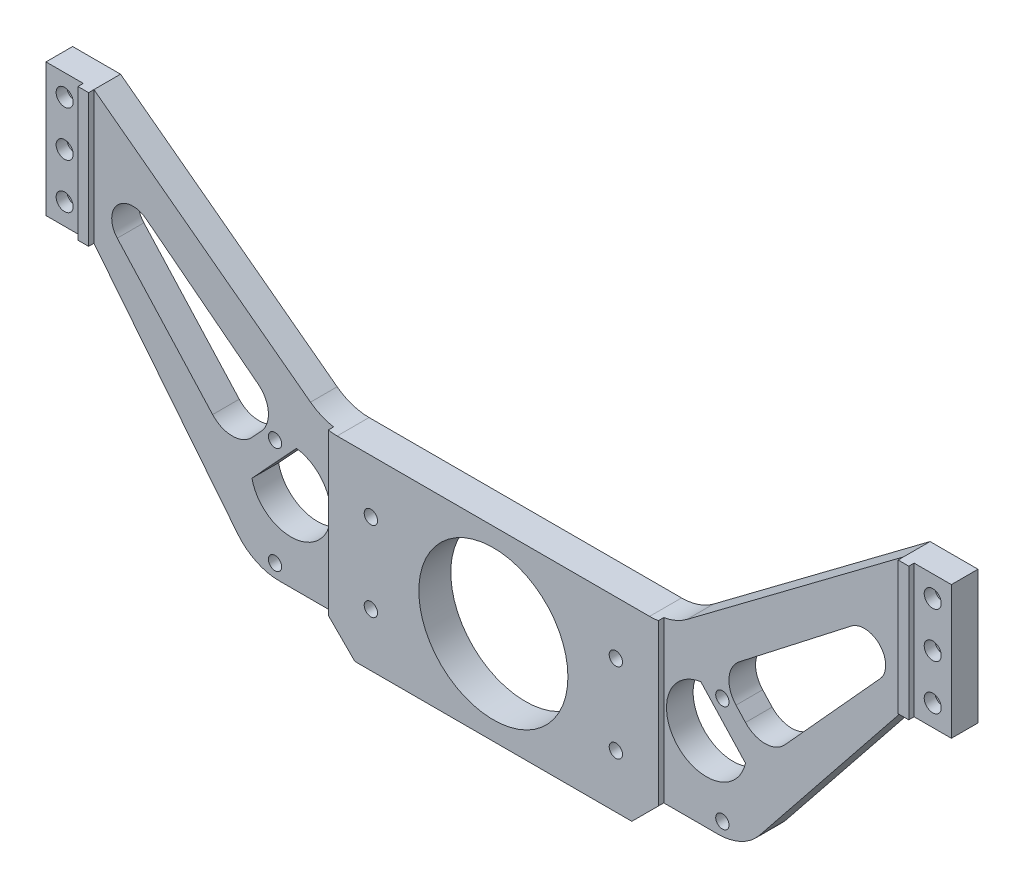
SolidWorks part; units mm, degrees
material "6061 合金"
ref_plane "前视基准面" through (0, 0, 0) normal (0, 0, 1) x (1, 0, 0)
ref_plane "上视基准面" through (0, 0, 0) normal (0, 1, 0) x (1, 0, 0)
ref_plane "右视基准面" through (0, 0, 0) normal (1, 0, 0) x (0, 0, -1)
sketch "草图1" plane through (0, 0, 0) normal (0, 0, 1) x (1, 0, 0)
  line L0 (0, 0) -> (0, 25) construction
  line L1 (-23, -7.5) -> (23, -7.5) construction
  line L2 (-23, -7.5) -> (-23, 7.5) construction
  line L3 (-23, 7.5) -> (23, 7.5) construction
  line L4 (23, -7.5) -> (23, 7.5) construction
  line L5 (-23, -7.5) -> (23, 7.5) construction
  line L6 (-23, 7.5) -> (23, -7.5) construction
  line L7 (-42, -10) -> (42, -10) construction
  line L8 (-42, -10) -> (-42, 10) construction
  line L9 (-42, 10) -> (42, 10) construction
  line L10 (42, -10) -> (42, 10) construction
  line L11 (-42, -10) -> (42, 10) construction
  line L12 (-42, 10) -> (42, -10) construction
  line L13 (-85, 25) -> (85, 25) construction
  line L14 (-85, 25) -> (-85, 50)
  line L15 (-85, 25) -> (-76, 25)
  line L16 (-76, 25) -> (-49.0024, -8.747)
  line L17 (-46, -12.5) -> (46, -12.5) construction
  line L18 (-46, -12.5) -> (-46, 12.5) construction
  line L19 (-46, 12.5) -> (46, 12.5) construction
  line L20 (46, -12.5) -> (46, 12.5) construction
  line L21 (-46, -12.5) -> (46, 12.5) construction
  line L22 (-46, 12.5) -> (46, -12.5) construction
  line L23 (-23, 7.5) -> (-23, 12.5) construction
  line L24 (-85, 50) -> (-76, 50)
  line L25 (-26, 12.5) -> (-26, -10) construction
  line L26 (-76, 50) -> (-35.3333, 19.5)
  line L27 (0, 17.5) -> (0, -17.5) construction
  line L28 (29.3333, 17.5) -> (-29.3333, 17.5)
  line L29 (26, -17.5) -> (-26, -17.5)
  line L30 (-26, -17.5) -> (-31, -12.5)
  line L31 (-31, -12.5) -> (-41.1938, -12.5)
  line L32 (26, -17.5) -> (31, -12.5)
  line L33 (31, -12.5) -> (41.1938, -12.5)
  line L34 (76, 50) -> (35.3333, 19.5)
  line L35 (76, 25) -> (49.0024, -8.747)
  line L36 (85, 25) -> (76, 25)
  line L37 (85, 25) -> (85, 50)
  line L38 (85, 50) -> (76, 50)
  circle A0 centre (0, 0) radius 14
  circle A1 centre (0, 0) radius 76 construction
  arc A2 (-29.3333, 17.5) -> (-35.3333, 19.5) centre (-29.3333, 27.5) cw
  arc A3 (-41.1938, -12.5) -> (-49.0024, -8.747) centre (-41.1938, -2.5) cw
  arc A4 (41.1938, -12.5) -> (49.0024, -8.747) centre (41.1938, -2.5) ccw
  arc A5 (29.3333, 17.5) -> (35.3333, 19.5) centre (29.3333, 27.5) ccw
  dimension "D1" = 28
  dimension "D13" = 152
  dimension "D15" = 10
  dimension "D2" = 15
  dimension "D3" = 46
  dimension "D4" = 84
  dimension "D5" = 20
  dimension "D6" = 170
  dimension "D7" = 25
  dimension "D8" = 25
  dimension "D9" = 9
  dimension "D10" = 25
  dimension "D11" = 4
  dimension "D12" = 3
  dimension "D14" = 35
extrude "凸台-拉伸1" add sketch "草图1" along normal blind 5
sketch "草图2" plane through (0, 0, 5) normal (0, 0, 1) x (1, 0, 0)
  line L0 (-76, 25) -> (-76, 50)
  line L1 (-76, 50) -> (-78, 50)
  line L2 (-76, 50) -> (-85, 50) construction
  line L3 (-78, 50) -> (-78, 25)
  line L4 (-85, 25) -> (-76, 25) construction
  line L5 (-78, 25) -> (-76, 25)
  line L6 (0, -17.5) -> (0, 44.7211) construction
  line L7 (-26, -17.5) -> (26, -17.5) construction
  line L8 (78, 25) -> (76, 25)
  line L9 (78, 50) -> (78, 25)
  line L10 (76, 50) -> (78, 50)
  line L11 (76, 25) -> (76, 50)
  dimension "D1" = 2
extrude "凸台-拉伸2" add sketch "草图2" along normal blind 1
sketch "草图3" plane through (0, 0, 5) normal (0, 0, 1) x (1, 0, 0)
  line L0 (-32.4956, 18.0132) -> (-45.5256, -11.513) construction
  line L1 (-76, 37.5) -> (-39.0106, 3.2501) construction
  line L2 (-76, 25) -> (-76, 50) construction
  line L3 (-71.6241, 28.0172) -> (-53.7145, 8.2889)
  line L4 (-66.2092, 33.8652) -> (-45.1638, 17.5235)
  line L5 (-48.6995, 2.7647) -> (-39.2707, 12.9476) construction
  line L6 (0, -17.5) -> (0, 17.5) construction
  line L7 (-26, -17.5) -> (26, -17.5) construction
  line L8 (29.3333, 17.5) -> (-29.3333, 17.5) construction
  line L9 (42, -10) -> (-42, -10) construction
  line L10 (42, -10) -> (42, 10) construction
  line L11 (42, 10) -> (-42, 10) construction
  line L12 (-42, -10) -> (-42, 10) construction
  line L13 (42, -10) -> (-42, 10) construction
  line L14 (42, 10) -> (-42, -10) construction
  line L15 (-46.3437, 8.2526) -> (-44.5616, 10.1773)
  line L16 (44.8786, 3.2115) -> (46.3354, 1.6382)
  line L17 (-44.8786, 3.2115) -> (-46.3354, 1.6382)
  line L18 (-37.966, 10.677) -> (-44.8786, 3.2115)
  line L19 (37.966, 10.677) -> (44.8786, 3.2115)
  line L20 (46.3437, 8.2526) -> (44.5616, 10.1773)
  line L21 (71.6241, 28.0172) -> (53.7145, 8.2889)
  line L22 (66.2092, 33.8652) -> (45.1638, 17.5235)
  arc A0 (-35.3333, 19.5) -> (-29.3333, 17.5) centre (-29.3333, 27.5) ccw construction
  arc A1 (-49.0024, -8.747) -> (-41.1938, -12.5) centre (-41.1938, -2.5) ccw construction
  arc A2 (-44.5637, -1.7911) -> (-34.4108, 9.1739) centre (-39.0106, 3.2501) ccw
  arc A3 (-66.2092, 33.8652) -> (-71.6241, 28.0172) centre (-68.6624, 30.7059) ccw
  arc A4 (-53.7145, 8.2889) -> (-46.3437, 8.2526) centre (-50.0124, 11.6497) ccw
  arc A5 (-45.1638, 17.5235) -> (-44.5616, 10.1773) centre (-48.2303, 13.5743) cw
  arc A6 (-44.5637, -1.7911) -> (-46.3354, 1.6382) centre (-39.0106, 3.2501) cw
  arc A7 (-34.4108, 9.1739) -> (-37.966, 10.677) centre (-39.0106, 3.2501) ccw
  arc A8 (34.4108, 9.1739) -> (37.966, 10.677) centre (39.0106, 3.2501) cw
  arc A9 (44.5637, -1.7911) -> (34.4108, 9.1739) centre (39.0106, 3.2501) cw
  arc A10 (44.5637, -1.7911) -> (46.3354, 1.6382) centre (39.0106, 3.2501) ccw
  arc A11 (45.1638, 17.5235) -> (44.5616, 10.1773) centre (48.2303, 13.5743) ccw
  arc A12 (53.7145, 8.2889) -> (46.3437, 8.2526) centre (50.0124, 11.6497) cw
  arc A13 (66.2092, 33.8652) -> (71.6241, 28.0172) centre (68.6624, 30.7059) cw
  point P24 (0, 0)
  dimension "D1" = 15
  dimension "D3" = 8
  dimension "D8" = 5
  dimension "D9" = 5
  dimension "D2" = 10
  dimension "D4" = 20
  dimension "D5" = 84
  dimension "D6" = 2
  dimension "D7" = 2.5
extrude "切除-拉伸2" cut sketch "草图3" against normal up to next
sketch "草图5" plane through (0, 0, 5) normal (0, 0, 1) x (1, 0, 0)
  line L1 (-42, -10) -> (42, -10) construction
  line L2 (-42, -10) -> (-42, 10) construction
  line L3 (-42, 10) -> (42, 10) construction
  line L4 (42, -10) -> (42, 10) construction
  line L5 (-42, -10) -> (42, 10) construction
  line L6 (-42, 10) -> (42, -10) construction
  point P0 (0, 0)
  dimension "D1" = 20
  dimension "D2" = 84
hole_wizard "M3 螺纹孔1" positions "3D草图1" profile "草图6" tap size "M3" standard "GB"
sketch3d "3D草图1"
  point P0 (-42, 10, 5)
  point P3 (-42, -10, 5)
  point P6 (42, 10, 5)
  point P9 (42, -10, 5)
sketch "草图6" plane through (-42, 10, 5) normal (1, 0, 0) x (0, -1, 0)
  line L0 (0, 0) -> (0, 9.2511)
  line L1 (0, 9.2511) -> (1.25, 8.5)
  line L2 (1.25, 8.5) -> (1.25, 0)
  line L5 (1.25, 0) -> (0, 0)
  line L10 (0, 9.2511) -> (-1.25, 8.5) construction
  line L11 (0, -6.35) -> (0, 107.95) construction
  dimension "螺纹孔钻头直径" = 2.5
  dimension "螺纹孔钻头深度" = 8.5
  dimension "导头角度" = 118
cosmetic thread "孔螺蚊线1" parameters "D1"=5, "D2"=3
cosmetic thread "孔螺蚊线2" parameters "D1"=5, "D2"=3
cosmetic thread "孔螺蚊线3" parameters "D1"=5, "D2"=3
cosmetic thread "孔螺蚊线4" parameters "D1"=5, "D2"=3
sketch "草图9" plane through (0, 0, 5) normal (0, 0, 1) x (1, 0, 0)
  line L0 (-31, -12.5) -> (-31, 17.6399)
  line L2 (31, -12.5) -> (31, 17.6399)
  line L3 (0, 0) -> (0, 30.8185) construction
  line L4 (-29.3333, 17.5) -> (29.3333, 17.5)
  line L7 (-31, -12.5) -> (-26, -17.5)
  line L8 (-26, -17.5) -> (26, -17.5)
  line L9 (26, -17.5) -> (31, -12.5)
  circle A0 centre (0, 0) radius 14
  arc A3 (-35.3333, 19.5) -> (-29.3333, 17.5) centre (-29.3333, 27.5) ccw construction
  arc A4 (29.3333, 17.5) -> (35.3333, 19.5) centre (29.3333, 27.5) ccw construction
  arc A5 (-31, 17.6399) -> (-29.3333, 17.5) centre (-29.3333, 27.5) ccw
  arc A6 (29.3333, 17.5) -> (31, 17.6399) centre (29.3333, 27.5) ccw
  dimension "D1" = 28
extrude "凸台-拉伸3" add sketch "草图9" along normal blind 1
sketch "草图10" plane through (0, 0, 6) normal (0, 0, 1) x (1, 0, 0)
  line L1 (-23, -7.5) -> (23, -7.5) construction
  line L2 (-23, -7.5) -> (-23, 7.5) construction
  line L3 (-23, 7.5) -> (23, 7.5) construction
  line L4 (23, -7.5) -> (23, 7.5) construction
  line L5 (-23, -7.5) -> (23, 7.5) construction
  line L6 (-23, 7.5) -> (23, -7.5) construction
  point P0 (0, 0)
  dimension "D1" = 46
  dimension "D2" = 15
hole_wizard "M3 螺纹孔3" positions "3D草图3" profile "草图11" tap size "M3" standard "GB"
sketch3d "3D草图3"
  point P0 (-23, 7.5, 6)
  point P3 (-23, -7.5, 6)
  point P6 (23, -7.5, 6)
  point P9 (23, 7.5, 6)
sketch "草图11" plane through (-23, 7.5, 6) normal (1, 0, 0) x (0, -1, 0)
  line L0 (0, 0) -> (0, 9.2511)
  line L1 (0, 9.2511) -> (1.25, 8.5)
  line L2 (1.25, 8.5) -> (1.25, 0)
  line L5 (1.25, 0) -> (0, 0)
  line L10 (0, 9.2511) -> (-1.25, 8.5) construction
  line L11 (0, -6.35) -> (0, 107.95) construction
  dimension "螺纹孔钻头直径" = 2.5
  dimension "螺纹孔钻头深度" = 8.5
  dimension "导头角度" = 118
cosmetic thread "孔螺蚊线9" parameters "D1"=6, "D2"=3
cosmetic thread "孔螺蚊线10" parameters "D1"=6, "D2"=3
cosmetic thread "孔螺蚊线11" parameters "D1"=6, "D2"=3
cosmetic thread "孔螺蚊线12" parameters "D1"=6, "D2"=3
sketch "草图12" plane through (0, 0, 5) normal (0, 0, 1) x (1, 0, 0)
  line L0 (-85, 37.5) -> (-78, 37.5) construction
  line L1 (-85, 50) -> (-85, 25) construction
  line L2 (-78, 50) -> (-78, 25) construction
  line L3 (-81.5, 37.5) -> (-81.5, 29) construction
  line L4 (0, 0) -> (0, 35.541) construction
  line L5 (81.5, 37.5) -> (81.5, 29) construction
  line L6 (85, 37.5) -> (78, 37.5) construction
  circle A0 centre (-81.5, 37.5) radius 1.6
  circle A1 centre (-81.5, 29) radius 1.6
  circle A2 centre (-81.5, 46) radius 1.6
  circle A3 centre (81.5, 46) radius 1.6
  circle A4 centre (81.5, 29) radius 1.6
  circle A5 centre (81.5, 37.5) radius 1.6
  dimension "D1" = 3.2
  dimension "D3" = 3.2
  dimension "D2" = 8.5
extrude "切除-拉伸3" cut sketch "草图12" against normal up to next
sketch "草图13" plane through (0, 0, 0) normal (0, 0, -1) x (-1, 0, 0)
  line L0 (0, -17.5) -> (0, 33.6135) construction
  line L1 (26, -17.5) -> (-26, -17.5) construction
  circle A0 centre (-81.5, 37.5) radius 3
  circle A1 centre (-81.5, 46) radius 3
  circle A2 centre (-81.5, 29) radius 3
  circle A3 centre (81.5, 29) radius 3
  circle A4 centre (81.5, 37.5) radius 3
  circle A5 centre (81.5, 46) radius 3
  dimension "D1" = 6
  dimension "D2" = 6
  dimension "D3" = 6
extrude "切除-拉伸4" cut sketch "草图13" against normal blind 3
